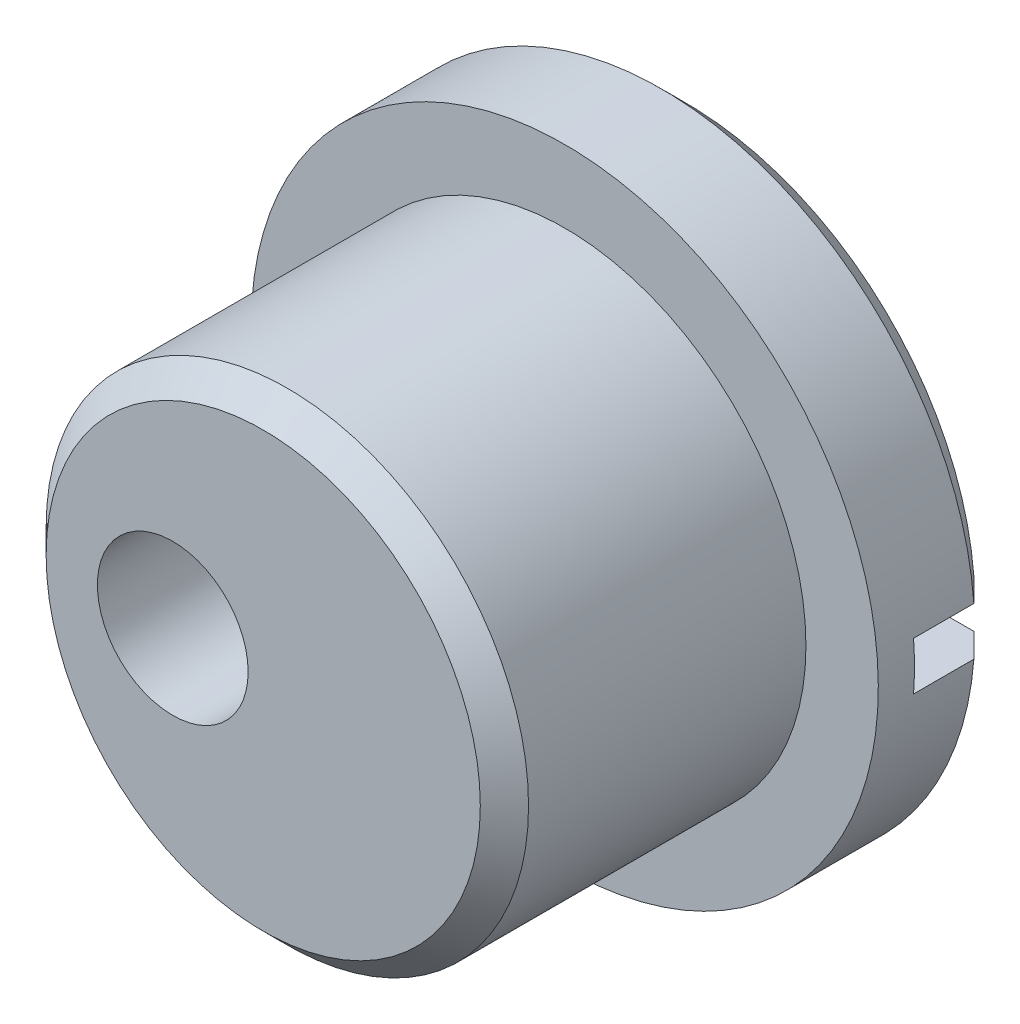
SolidWorks part; units mm, degrees
ref_plane "Front Plane" through (0, 0, 0) normal (0, 0, 1) x (1, 0, 0)
ref_plane "Top Plane" through (0, 0, 0) normal (0, 1, 0) x (1, 0, 0)
ref_plane "Right Plane" through (0, 0, 0) normal (1, 0, 0) x (0, 0, -1)
sketch "Sketch1" plane through (0, 0, 0) normal (0, 0, 1) x (1, 0, 0)
  circle A0 centre (1.5, 95.9979) radius 4 construction
  circle A1 centre (1.5, 95.9979) radius 4
extrude "Boss-Extrude1" add sketch "Sketch1" along normal up to vertex (5 mm away)
sketch "Sketch2" plane through (0, 0, 0) normal (0, 0, -1) x (-1, 0, 0)
  circle A0 centre (-1.5, 95.9979) radius 5.2
  circle A1 centre (-1.5, 95.9979) radius 4 construction
  dimension "D1" = 1.2
extrude "Boss-Extrude2" add sketch "Sketch2" along normal blind 2
sketch "Sketch3" plane through (0, 0, 5) normal (0, 0, 1) x (1, 0, 0)
  circle A0 centre (0, 95.9979) radius 1.25 construction
  circle A3 centre (0, 95.9979) radius 1.25
extrude "Cut-Extrude2" cut sketch "Sketch3" against normal through all
chamfer "Chamfer1" distance 0.4 angle 45 2 edges at (-3.7, 95.9979, -2) (5.5, 95.9979, 5)
sketch "Sketch4" plane through (0, 0, -2) normal (0, 0, -1) x (-1, 0, 0)
  line L1 (-11.5, 96.3979) -> (8.5, 96.3979)
  line L2 (-11.5, 96.3979) -> (-11.5, 95.5979)
  line L3 (-11.5, 95.5979) -> (8.5, 95.5979)
  line L4 (8.5, 96.3979) -> (8.5, 95.5979)
  point P4 (-1.5, 96.3979)
  point P5 (-1.5, 95.9979)
  point P6 (0, 0)
  point P8 (8.5, 95.9979)
  dimension "D1" = 0.8
  dimension "D2" = 20
extrude "Cut-Extrude3" cut sketch "Sketch4" against normal blind 1.4
sketch "Sketch5" plane through (0, 0, -2) normal (0, 0, -1) x (-1, 0, 0)
  circle A0 centre (0, 95.9979) radius 2
  dimension "D1" = 4
extrude "Cut-Extrude4" cut sketch "Sketch5" against normal blind 2.5
fillet "Fillet1" radius 0.5 1 edges at (-2, 95.9979, 0.5)
